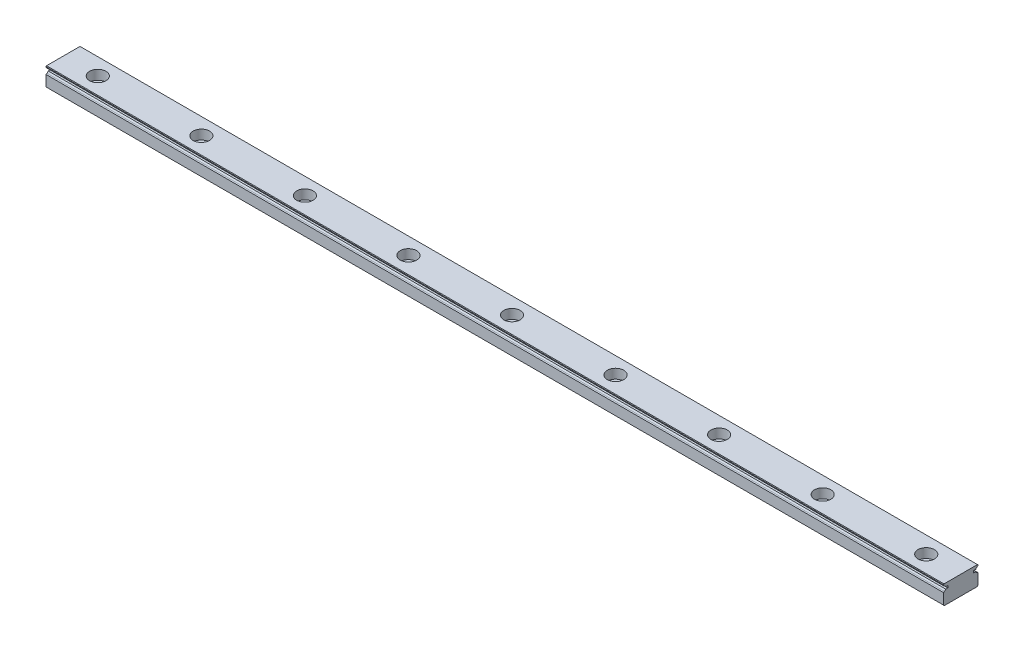
SolidWorks part; units mm, degrees
ref_plane "Front Plane" through (0, 0, 0) normal (0, 0, 1) x (1, 0, 0)
ref_plane "Top Plane" through (0, 0, 0) normal (0, 1, 0) x (1, 0, 0)
ref_plane "Right Plane" through (0, 0, 0) normal (1, 0, 0) x (0, 0, -1)
ref_plane "Plane1" through (-20, 0, 0) normal (1, 0, 0) x (0, 0, -1)
sketch "Sketch1" plane through (-20, 0, 0) normal (1, 0, 0) x (0, 0, -1)
  line L0 (0, 11) -> (0, 0) construction
  line L1 (-10, 11) -> (10, 11)
  line L3 (-10, 0) -> (10, 0)
  line L10 (10, 11) -> (10, 0)
  line L11 (-10, 11) -> (-10, 0)
  dimension "H1" = 11
  dimension "W1" = 20
extrude "Boss-Extrude1" add sketch "Sketch1" along normal blind 520
sketch "Sketch2" plane through (-20, 0, 0) normal (1, 0, 0) x (0, 0, -1)
  line L0 (7.5, 8.5) -> (10, 8.5) construction
  line L1 (0, 0) -> (0, 9.1) construction
  line L2 (10, 10.221) -> (9.4553, 9.9114)
  line L3 (7.5, 9.1) -> (8.7205, 9.1)
  line L4 (7.5, 9.1) -> (7.5, 7.9)
  line L5 (7.5, 7.9) -> (8.725, 7.9)
  line L6 (10, 6.779) -> (9.4348, 7.1104)
  line L7 (10, 11) -> (10, 0) construction
  line L8 (10, 10.221) -> (10, 6.779)
  line L9 (-10, 0) -> (10, 0) construction
  line L10 (-7.5, 8.5) -> (-10, 8.5) construction
  line L11 (-10, 10.221) -> (-10, 6.779)
  line L12 (-10, 6.779) -> (-9.4348, 7.1104)
  line L13 (-7.5, 7.9) -> (-8.725, 7.9)
  line L14 (-7.5, 9.1) -> (-7.5, 7.9)
  line L15 (-7.5, 9.1) -> (-8.7205, 9.1)
  line L16 (-10, 10.221) -> (-9.4553, 9.9114)
  arc A0 (9.4553, 9.9114) -> (8.7205, 9.1) centre (10.32, 8.39) ccw
  arc A1 (8.725, 7.9) -> (9.4348, 7.1104) centre (10.32, 8.62) ccw
  arc A2 (-8.725, 7.9) -> (-9.4348, 7.1104) centre (-10.32, 8.62) cw
  arc A3 (-9.4553, 9.9114) -> (-8.7205, 9.1) centre (-10.32, 8.39) cw
  dimension "MSM_8" = 1.75
  dimension "MSM_6" = 8.5
  dimension "MSM_7" = 60
  dimension "MSM_2" = 0.32
  dimension "MSM_5" = 1.2
  dimension "MSM_1" = 2.5
  dimension "MSM_3" = 8.62
  dimension "MSM_4" = 8.39
extrude "Cut-Extrude1" cut sketch "Sketch2" along normal through all
hole_wizard "CBORE for Socket Head Cap Screw1" positions "Sketch4" profile "Sketch3" counterbore size "M3" standard "JIS" end condition through all
sketch "Sketch4" plane through (0, 11, 0) normal (0, 1, 0) x (1, 0, 0)
  line L0 (-20, -3.025) -> (-20, 3.025) construction
  point P0 (0, 0)
  dimension "G" = 20
sketch "Sketch3" plane through (0, 11, 0) normal (1, 0, 0) x (0, 0, 1)
  line L0 (0, 0) -> (0, 11)
  line L1 (0, 11) -> (3, 11)
  line L3 (3, 11) -> (3, 5.5)
  line L4 (3, 5.5) -> (4.75, 5.5)
  line L5 (4.75, 5.5) -> (4.75, 0)
  line L7 (4.75, 0) -> (0, 0)
  line L11 (0, 0) -> (0, 11) construction
  dimension "D1_s" = 6
  dimension "Thru Hole Depth" = 11
  dimension "D2_s" = 9.5
  dimension "H_s" = 5.5
pattern_linear "LPattern1" count 9 spacing 60 along (1, 0, 0) of "CBORE for Socket Head Cap Screw1"
chamfer "Chamfer1" distance 0.3 2 edges at (240, 11, 10) (240, 11, -10)
chamfer "Chamfer2" distance 0.5 2 edges at (240, 0, -10) (240, 0, 10)
ref_plane "Plane2" [suppressed] through (0, 5.5, 0) normal (0, 1, 0) x (1, 0, 0)
hole_wizard "Tap1" [suppressed] positions "Sketch6" profile "Sketch5" hole size "M3x0.5" standard "JIS"
sketch "Sketch6" [suppressed] plane through (0, 5.5, 0) normal (0, 1, 0) x (1, 0, 0)
  line L0 (-7.5, -3.025) -> (-7.5, 3.025) construction
  point P0 (0, 0)
  dimension "G" = 20
sketch "Sketch5" [suppressed] plane through (0, 5.5, 0) normal (1, 0, 0) x (0, 0, 1)
  line L0 (0, 0) -> (0, 5.5)
  line L1 (0, 5.5) -> (1.621, 5.5)
  line L2 (1.621, 5.5) -> (1.621, 0)
  line L5 (1.621, 0) -> (0, 0)
  line L11 (0, 0) -> (0, 5.5) construction
  dimension "STD_1" = 3.242
  dimension "Thru Hole Depth" = 5.5
cosmetic thread "Thread1" [suppressed] parameters "MC"=4
pattern_linear "LPattern2" [suppressed]
sketch "Sketch7" [suppressed] plane through (0, 0, 0) normal (0, 0, 1) x (1, 0, 0)
  line L0 (-7.5, -3.025) -> (-7.5, 3.025) construction
  line L1 (-7.5, 5.5) -> (-5, 5.5)
  line L2 (-7.5, 5.5) -> (-7.5, 0)
  line L3 (-7.5, 0) -> (-5, 0)
  line L4 (-5, 5.5) -> (-5, 0)
  line L5 (0, 5.5) -> (0, 0) construction
  dimension "LLC" = 2.5
  dimension "N" = 5
extrude "Cut-Extrude2" [suppressed] cut sketch "Sketch7" against normal through all and the other way through all
sketch "Sketch8" [suppressed] plane through (0, 0, 0) normal (0, 0, 1) x (1, 0, 0)
  line L0 (-7.5, 5.5) -> (-7.5, 0) construction
  line L1 (45, 5.5) -> (47.5, 5.5)
  line L2 (45, 5.5) -> (45, 0)
  line L3 (45, 0) -> (47.5, 0)
  line L4 (47.5, 5.5) -> (47.5, 0)
  line L5 (-7.5, -3.025) -> (-7.5, 3.025) construction
  line L8 (40, 5.5) -> (40, 0) construction
  dimension "L" = 520
  dimension "RLC" = 2.5
  dimension "N" = 5
extrude "Cut-Extrude3" [suppressed] cut sketch "Sketch8" against normal through all and the other way through all
